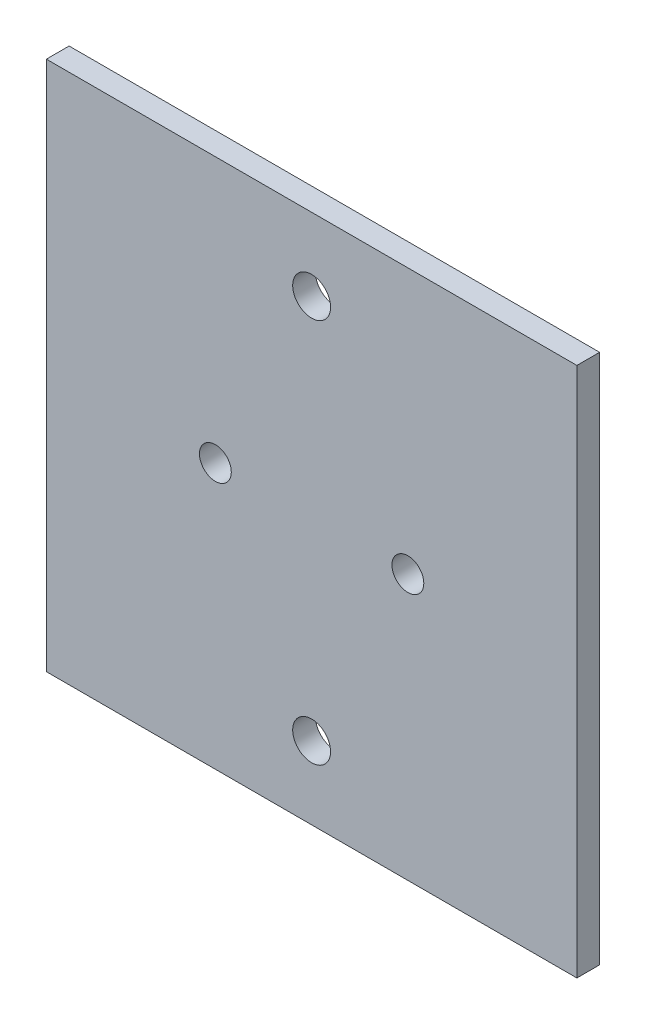
SolidWorks part; units mm, degrees
ref_plane "Alzado" through (0, 0, 0) normal (0, 0, 1) x (1, 0, 0)
ref_plane "Planta" through (0, 0, 0) normal (0, 1, 0) x (1, 0, 0)
ref_plane "Vista lateral" through (0, 0, 0) normal (1, 0, 0) x (0, 0, -1)
sketch "Croquis1" plane through (0, 0, 0) normal (0, 0, 1) x (1, 0, 0)
  line L0 (0, 0) -> (0, 25.4) construction
  line L1 (-35, 35) -> (35, 35)
  line L2 (-35, 35) -> (-35, -35)
  line L3 (-35, -35) -> (35, -35)
  line L4 (35, 35) -> (35, -35)
  line L5 (-35, 35) -> (35, -35) construction
  line L6 (-35, -35) -> (35, 35) construction
  line L7 (0, 0) -> (0, -25.4) construction
  circle A0 centre (0, 25.4) radius 2.5
  circle A1 centre (0, -25.4) radius 2.5
  point P0 (0, 0)
  dimension "D3" = 5
  dimension "D4" = 5
  dimension "D1" = 70
  dimension "D2" = 70
  dimension "D5" = 25.4
  dimension "D6" = 25.4
extrude "Saliente-Extruir1" add sketch "Croquis1" along normal blind 3
sketch "Croquis2" plane through (0, 0, 3) normal (0, 0, 1) x (1, 0, 0)
  line L0 (0, 0) -> (-12.7, 0) construction
  line L1 (0, 0) -> (12.7, 0) construction
  circle A0 centre (-12.7, 0) radius 2.1
  circle A1 centre (12.7, 0) radius 2.1
  dimension "D3" = 4.2
  dimension "D4" = 4.2
  dimension "D1" = 12.7
  dimension "D2" = 12.7
extrude "Cortar-Extruir1" cut sketch "Croquis2" against normal up to next
